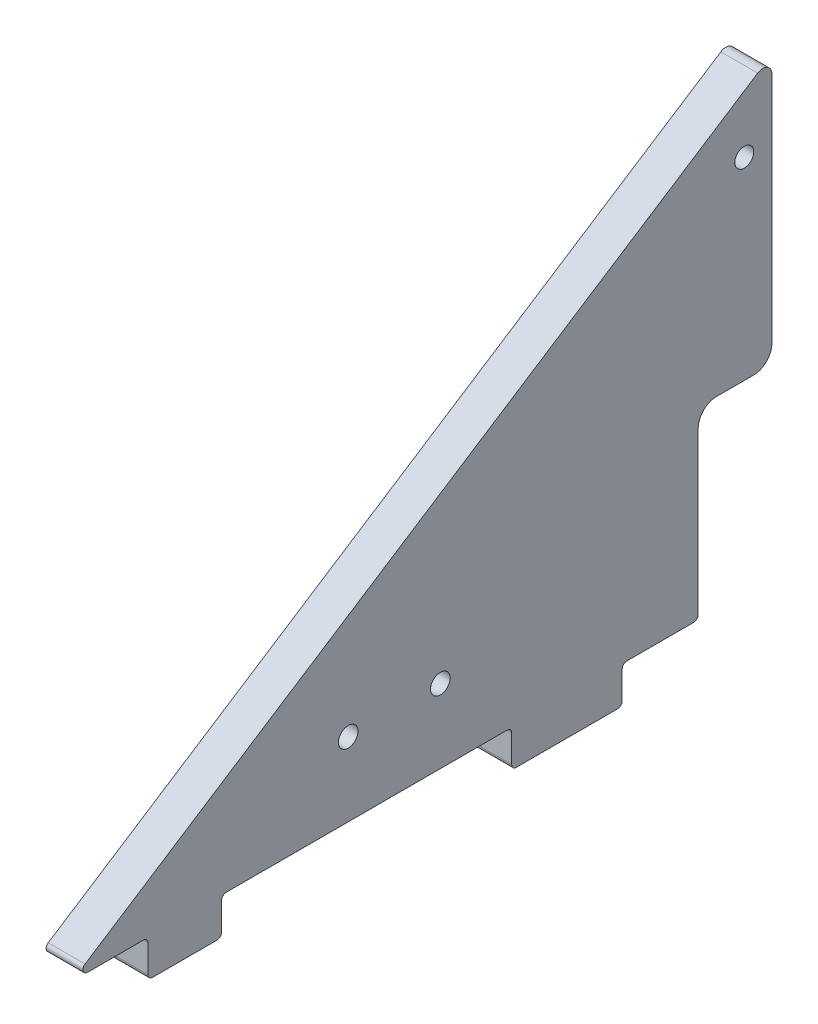
SolidWorks part; units mm, degrees
material "PE High Density"
ref_plane "Front Plane" through (0, 0, 0) normal (0, 0, 1) x (1, 0, 0)
ref_plane "Top Plane" through (0, 0, 0) normal (0, 1, 0) x (1, 0, 0)
ref_plane "Right Plane" through (0, 0, 0) normal (1, 0, 0) x (0, 0, -1)
sketch "Sketch1" plane through (0, 0, 0) normal (1, 0, 0) x (0, 0, -1)
  line L0 (0, 0) -> (-215.9, 0)
  line L1 (-215.9, 0) -> (0, 139.7)
  line L2 (0, 139.7) -> (0, 0)
  line L3 (-135.4818, 0) -> (-135.4818, 38.1) construction
  line L4 (-26.1937, 0) -> (-64.2937, 0)
  line L5 (-26.1937, 0) -> (-26.1937, -12.7)
  line L6 (-26.1937, -12.7) -> (-64.2937, -12.7)
  line L7 (-64.2937, 0) -> (-64.2937, -12.7)
  line L8 (-164.3062, 0) -> (-189.7062, 0)
  line L9 (-164.3062, 0) -> (-164.3062, -12.7)
  line L10 (-164.3062, -12.7) -> (-189.7062, -12.7)
  line L11 (-189.7062, 0) -> (-189.7062, -12.7)
  line L12 (-135.4818, 38.1) -> (-84.6818, 38.1) construction
  line L13 (-84.6818, 38.1) -> (-84.6818, 0) construction
  dimension "D1" = 12.7
  dimension "D2" = 215.9
  dimension "D3" = 139.7
  dimension "D4" = 26.1937
  dimension "D5" = 26.1937
  dimension "D6" = 25.4
  dimension "D7" = 38.1
  dimension "D8" = 38.1
  dimension "D9" = 50.8
extrude "Boss-Extrude1" add sketch "Sketch1" along normal mid plane 12.7 contours L2 L1 L0 | L0 L7 L6 L5 | L0 L11 L10 L9
sketch "Sketch10" plane through (6.35, 0, 0) normal (1, 0, 0) x (0, 0, -1)
  line L0 (-64.2937, 0) -> (-164.3062, 0) construction
  line L1 (-133.35, 0) -> (-76.2, 0)
  line L2 (-133.35, 0) -> (-133.35, 38.1)
  line L3 (-133.35, 38.1) -> (-76.2, 38.1)
  line L4 (-76.2, 0) -> (-76.2, 38.1)
  line L5 (-120.65, 25.4) -> (-88.9, 25.4)
  line L6 (-104.775, 25.4) -> (-104.775, 0) construction
  line L7 (0, 139.7) -> (0, 0) construction
  dimension "D1" = 25.4
  dimension "D2" = 31.75
  dimension "D3" = 38.1
  dimension "D4" = 57.15
  dimension "D5" = 76.2
hole_wizard "1/4 Clearance Hole1" positions "Sketch11" profile "Sketch12" hole size "1/4" standard "ANSI Inch" end condition up to next
sketch "Sketch11" plane through (6.35, 0, 0) normal (1, 0, 0) x (0, 0, -1)
  point P0 (-88.9, 25.4)
  point P3 (-120.65, 25.4)
sketch "Sketch12" plane through (6.35, 25.4, 88.9) normal (0, 1, 0) x (0, 0, -1)
  line L0 (0, 0) -> (0, 12.7)
  line L1 (0, 12.7) -> (3.3782, 12.7)
  line L2 (3.3782, 12.7) -> (3.3782, 0)
  line L5 (3.3782, 0) -> (0, 0)
  line L11 (0, -6.35) -> (0, 107.95) construction
  dimension "Thru Hole Dia." = 6.7564
  dimension "Thru Hole Depth" = 12.7
sketch "Sketch13" plane through (-6.35, 0, 0) normal (-1, 0, 0) x (0, 0, 1)
  line L0 (-38.1, 40.0128) -> (-38.1, -49959.9872) construction
  line L1 (-25.4, 156.1353) -> (0, 139.7)
  line L2 (215.9, 0) -> (0, 139.7) construction
  line L3 (-25.4, 156.1353) -> (-25.4, 63.5)
  line L4 (-25.4, 63.5) -> (0, 63.5)
  line L5 (0, 139.7) -> (0, 0) construction
  line L6 (0, 63.5) -> (0, 139.7)
  line L7 (0, 0) -> (26.1937, 0) construction
  dimension "D1" = 254
  dimension "D2" = 12.7
  dimension "D3" = 63.5
extrude "Boss-Extrude2" add sketch "Sketch13" against normal through all
fillet "top fillet" radius 3.175 1 edges at (0, 156.1353, -25.4)
fillet "bottom fillets" radius 1.5875 10 edges at (0, 0, 0) (0, 0, 26.1937) (0, -12.7, 26.1937) (0, -12.7, 64.2937) (0, 0, 64.2937) (0, 0, 164.3062) (0, -12.7, 164.3062) (0, -12.7, 189.7062) (0, 0, 189.7062) (0, 0, 215.9)
sketch "Sketch5" plane through (6.35, 0, 0) normal (1, 0, 0) x (0, 0, -1)
  line L1 (-1.5875, 0) -> (-24.6062, 0) construction
  line L2 (25.4, 150.2992) -> (25.4, 63.5) construction
  point P0 (15.875, 130.175)
  dimension "D1" = 9.525
  dimension "D2" = 130.175
hole_wizard "1/4 Clearance Hole2" positions "Sketch6" profile "Sketch7" hole size "1/4" standard "ANSI Inch" end condition up to next
sketch "Sketch6" plane through (6.35, 0, 0) normal (1, 0, 0) x (0, 0, -1)
  point P0 (15.875, 130.175)
sketch "Sketch7" plane through (6.35, 130.175, -15.875) normal (0, 1, 0) x (0, 0, -1)
  line L0 (0, 0) -> (0, 12.7)
  line L1 (0, 12.7) -> (3.2639, 12.7)
  line L2 (3.2639, 12.7) -> (3.2639, 0)
  line L5 (3.2639, 0) -> (0, 0)
  line L11 (0, -6.35) -> (0, 107.95) construction
  dimension "Thru Hole Dia." = 6.5278
  dimension "Thru Hole Depth" = 12.7
fillet "Fillet1" radius 6.35 2 edges at (0, 63.5, -25.4) (0, 63.5, 0)
